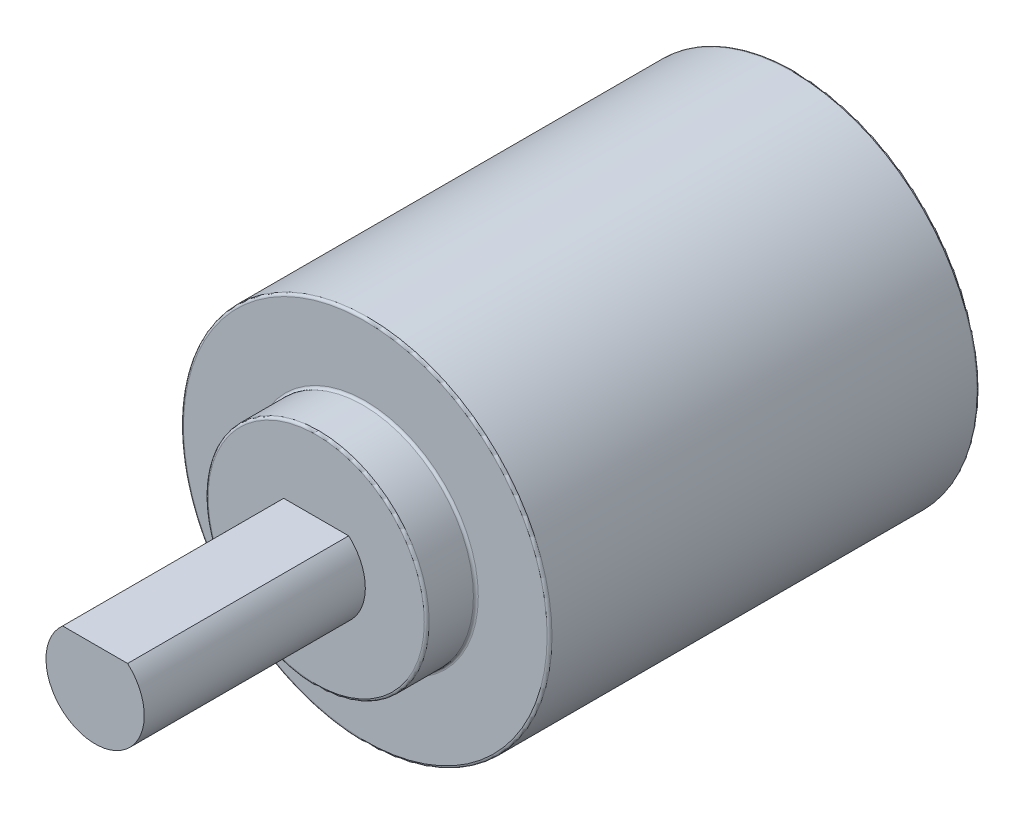
SolidWorks part; units mm, degrees
ref_plane "Front" through (0, 0, 0) normal (0, 0, 1) x (1, 0, 0)
ref_plane "Top" through (0, 0, 0) normal (0, 1, 0) x (1, 0, 0)
ref_plane "Right" through (0, 0, 0) normal (1, 0, 0) x (0, 0, -1)
sketch "Esquisse1" plane through (0, 0, 0) normal (0, 0, 1) x (1, 0, 0)
  circle A0 centre (0, 0) radius 15
  dimension "D1" = 30
extrude "Boss.-Extru.1" add sketch "Esquisse1" along normal blind 35
sketch "Esquisse2" plane through (0, 0, 35) normal (0, 0, 1) x (1, 0, 0)
  circle A0 centre (0, 0) radius 9
  dimension "D1" = 18
extrude "Boss.-Extru.2" add sketch "Esquisse2" along normal blind 4
sketch "Esquisse3" plane through (0, 0, 39) normal (0, 0, 1) x (1, 0, 0)
  line L0 (-2.6458, 3) -> (2.6458, 3)
  line L1 (-2.8385, -4) -> (1.7277, -4) construction
  circle A0 centre (0, 0) radius 4
  dimension "D1" = 8
  dimension "D2" = 7
extrude "Boss.-Extru.3" add sketch "Esquisse3" along normal blind 18 contours L0 A0
sketch "Esquisse4" plane through (0, 0, 0) normal (0, 0, -1) x (-1, 0, 0)
  circle A0 centre (0, 0) radius 10
  dimension "D1" = 20
extrude "Enlèv. mat.-Extru.1" cut sketch "Esquisse4" against normal blind 18
fillet "Congé1" radius 0.2 5 edges at (9, 0, 39) (15, 0, 35) (9, 0, 35) (15, 0, 0) (-10, 0, 0)
fillet "Congé2" radius 0.5 1 edges at (-10, 0, 18)
